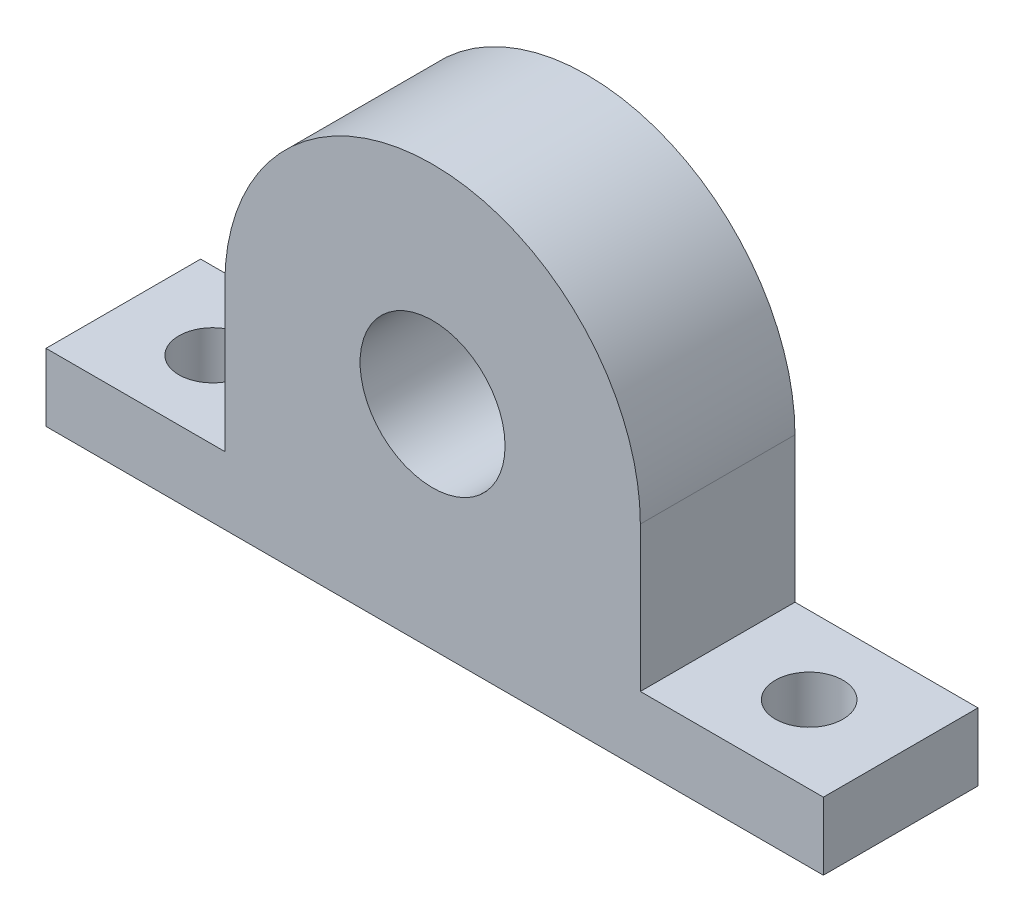
SolidWorks part; units mm, degrees
ref_plane "前视基准面" through (0, 0, 0) normal (0, 0, 1) x (1, 0, 0)
ref_plane "上视基准面" through (0, 0, 0) normal (0, 1, 0) x (1, 0, 0)
ref_plane "右视基准面" through (0, 0, 0) normal (1, 0, 0) x (0, 0, -1)
sketch "草图1" plane through (0, 0, 0) normal (0, 0, 1) x (1, 0, 0)
  line L0 (0, 21.5) -> (0, -21.5) construction
  line L1 (0, 0) -> (0, -22) construction
  line L2 (0, -22) -> (40, -22)
  line L3 (40, -22) -> (-40, -22)
  line L4 (-21.5, 0) -> (-21.5, -15)
  line L5 (-40, -22) -> (40.4399, -22)
  line L6 (-40, -22) -> (-40, -15)
  line L7 (-40, -15) -> (40.4399, -15)
  line L8 (40.4399, -22) -> (40.4399, -15)
  line L9 (21.5, 0) -> (21.5, -15)
  circle A0 centre (0, 0) radius 7.5
  circle A1 centre (0, 0) radius 21.5
  dimension "D1" = 15
  dimension "D2" = 43
  dimension "D3" = 22
  dimension "D4" = 80
  dimension "D5" = 40
  dimension "D6" = 7
extrude "凸台-拉伸2" add sketch "草图1" along normal blind 16 contours A1 L7 L9 | A1 L7 A0 | A1 L4 L7 | A1 L7 L6 L3 L2 L5 L8 | L7 A1
ref_plane "基准面1" through (0, -15, 0) normal (0, 1, 0) x (1, 0, 0)
sketch "草图2" plane through (0, -15, 0) normal (0, 1, 0) x (1, 0, 0)
  circle A0 centre (-30.75, -8) radius 3.5
  circle A1 centre (30.97, -8) radius 3.5
  dimension "D1" = 7
  dimension "D2" = 7
extrude "切除-拉伸1" cut sketch "草图2" against normal blind 16
